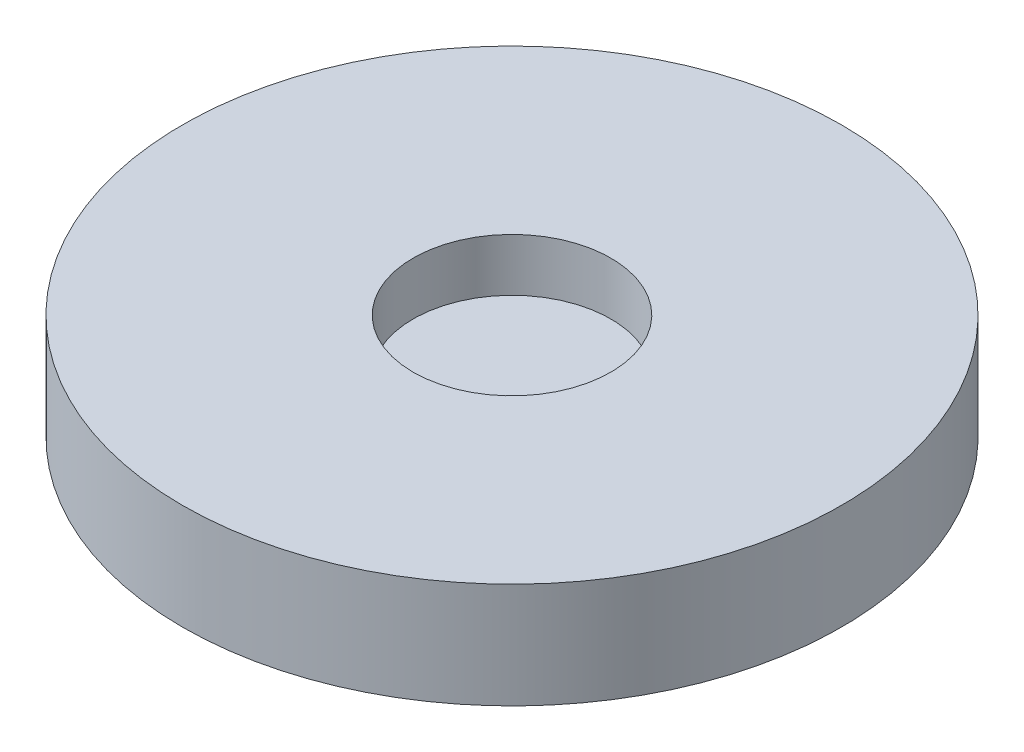
SolidWorks part; units mm, degrees
material "ABS"
ref_plane "Front Plane" through (0, 0, 0) normal (0, 0, 1) x (1, 0, 0)
ref_plane "Top Plane" through (0, 0, 0) normal (0, 1, 0) x (1, 0, 0)
ref_plane "Right Plane" through (0, 0, 0) normal (1, 0, 0) x (0, 0, -1)
sketch "Sketch1" plane through (0, 0, 0) normal (0, 1, 0) x (1, 0, 0)
  line L1 (30, -30) -> (-30, -30) construction
  line L2 (30, -30) -> (30, 30) construction
  line L3 (30, 30) -> (-30, 30) construction
  line L4 (-30, -30) -> (-30, 30) construction
  line L5 (30, -30) -> (-30, 30) construction
  line L6 (30, 30) -> (-30, -30) construction
  circle A0 centre (0, 0) radius 25
  point P0 (0, 0)
  dimension "D3" = 50
  dimension "D1" = 60
  dimension "D2" = 60
extrude "Boss-Extrude1" add sketch "Sketch1" along normal blind 8
sketch "Sketch2" plane through (0, 8, 0) normal (0, 1, 0) x (1, 0, 0)
  circle A0 centre (0, 0) radius 7.5
  dimension "D1" = 15
extrude "Cut-Extrude1" cut sketch "Sketch2" against normal blind 4
